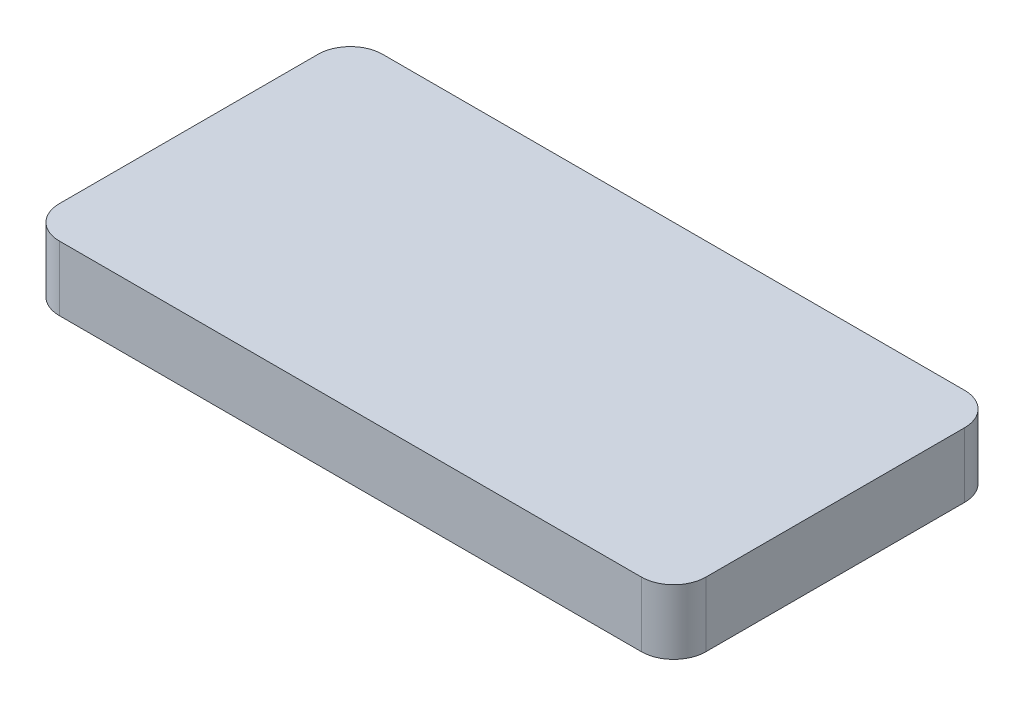
SolidWorks part; units mm, degrees
ref_plane "Front Plane" through (0, 0, 0) normal (0, 0, 1) x (1, 0, 0)
ref_plane "Top Plane" through (0, 0, 0) normal (0, 1, 0) x (1, 0, 0)
ref_plane "Right Plane" through (0, 0, 0) normal (1, 0, 0) x (0, 0, -1)
sketch "Sketch1" plane through (0, 0, 0) normal (0, 1, 0) x (1, 0, 0)
  line L0 (84.3058, 24.9827) -> (-15.6942, 24.9827) construction
  line L1 (79.3058, 49.9827) -> (-10.6942, 49.9827)
  line L2 (79.3058, -0.0173) -> (-10.6942, -0.0173)
  line L3 (84.3058, 44.9827) -> (84.3058, 4.9827)
  line L4 (-15.6942, 44.9827) -> (-15.6942, 4.9827)
  line L5 (84.3058, -0.0173) -> (-15.6942, -0.0173) construction
  line L6 (84.3058, 49.9827) -> (-15.6942, 49.9827) construction
  arc A0 (79.3058, -0.0173) -> (84.3058, 4.9827) centre (79.3058, 4.9827) ccw
  arc A1 (84.3058, 44.9827) -> (79.3058, 49.9827) centre (79.3058, 44.9827) ccw
  arc A2 (-10.6942, -0.0173) -> (-15.6942, 4.9827) centre (-10.6942, 4.9827) cw
  arc A3 (-10.6942, 49.9827) -> (-15.6942, 44.9827) centre (-10.6942, 44.9827) ccw
  point P18 (0, 0)
  dimension "D4" = 5
  dimension "D1" = 100
  dimension "D2" = 25
  dimension "D3" = 25
extrude "Boss-Extrude1" add sketch "Sketch1" along normal blind 10
sketch "Sketch2" plane through (0, 10, 0) normal (0, 1, 0) x (1, 0, 0)
  line L0 (-10.6942, -0.0173) -> (79.3058, -0.0173) construction
  line L1 (-10.6942, 21.5892) -> (9.2336, 21.5892)
  line L2 (-10.6942, 21.5892) -> (-10.6942, 4.9827)
  line L3 (-10.6942, 4.9827) -> (9.2336, 4.9827)
  line L4 (9.2336, 21.5892) -> (9.2336, 4.9827)
  line L5 (-10.6942, 21.5892) -> (9.2336, 4.9827) construction
  line L6 (-10.6942, 4.9827) -> (9.2336, 21.5892) construction
  line L7 (-15.6942, 44.9827) -> (-15.6942, 4.9827) construction
  line L8 (79.3058, 49.9827) -> (-10.6942, 49.9827) construction
  line L9 (84.3058, 4.9827) -> (84.3058, 44.9827) construction
  point P0 (-0.7303, 13.2859)
  dimension "D1" = 5
  dimension "D2" = 5
  dimension "D3" = 28.3935
  dimension "D4" = 75.0722
extrude "Boss-Extrude2" add sketch "Sketch2" against normal blind 6 separate body contours L2 L1 L4 L3
